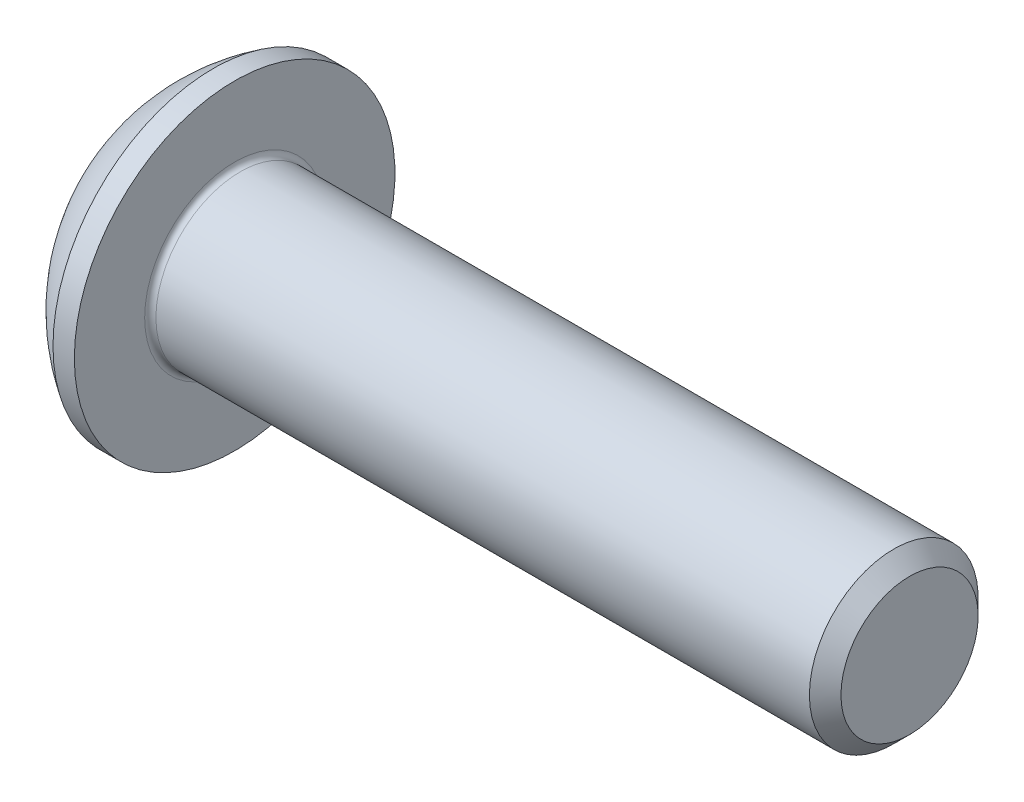
SolidWorks part; units mm, degrees
ref_plane "Plane1" through (0, 0, 0) normal (0, 0, 1) x (1, 0, 0)
ref_plane "Plane2" through (0, 0, 0) normal (0, 1, 0) x (1, 0, 0)
ref_plane "Plane3" through (0, 0, 0) normal (1, 0, 0) x (0, 0, -1)
sketch "BodySke" plane through (0, 0, 0) normal (0, 0, 1) x (1, 0, 0)
  line L0 (13.65, 0) -> (13.65, 1.2195)
  line L1 (13.3695, 1.5) -> (1.65, 1.5)
  line L2 (1.65, 1.5) -> (1.65, 2.85)
  line L3 (1.65, 2.85) -> (1.27, 2.85)
  line L4 (0, 0) -> (101.6, 0) construction
  line L5 (1.65, -2.85) -> (1.27, -2.85) construction
  line L6 (55.6768, -1.5) -> (1.65, -1.5) construction
  line L7 (13.65, 0) -> (0, 0)
  line L8 (0, 1.425) -> (0, -1.425) construction
  line L9 (0, 0) -> (0, 1.425)
  line L10 (13.65, 1.2195) -> (13.3695, 1.5)
  line L11 (13.65, -1.2195) -> (13.3695, -1.5) construction
  line L12 (2.15, 9.525) -> (2.15, -1.5) construction
  line L13 (1.65, 9.525) -> (1.65, -1.5) construction
  arc A1 (0, 1.425) -> (1.27, 2.85) centre (3.0334, 0) cw
  dimension "Diameter" = 3
  dimension "Length" = 12
  dimension "Head_dia" = 5.7
  dimension "D1" = 2.85
  dimension "Head_ht" = 1.65
  dimension "Head_side_ht" = 0.38
  dimension "Minor_dia" = 2.439
  dimension "Body_ch_ang" = 45
  dimension "Advance" = 0.5
  dimension "Thread_nom" = 12
revolve "BaseBody" add sketch "BodySke" angle 360 about L4
cosmetic thread "ThreadCosmetic" parameters "Thread_length"=11, "Thread_minor"=2.439
fillet "Fillet1" radius 0.1 1 edges at (1.65, 0, 1.5)
sketch "Sketch2" plane through (0, 0, 0) normal (0, 0, 1) x (1, 0, 0)
  line L0 (0, 1) -> (1.04, 1)
  line L1 (1.04, 1) -> (1.6174, 0)
  line L3 (1.6174, 0) -> (0, 0)
  line L4 (0, 0) -> (0, 1)
  line L5 (0, -1) -> (1.04, -1) construction
  line L6 (0, 0) -> (47.625, 0) construction
  dimension "D2" = 60
  dimension "PreBroach_depth" = 1.04
  dimension "PreBroach_dia" = 2
revolve "PreBroach" cut sketch "Sketch2" angle 360 about L6
sketch "Sketch3" plane through (0, 0, 0) normal (1, 0, 0) x (0, 0, -1)
  line L0 (-1, -0.5774) -> (-1, 0.5774)
  line L1 (-1, 0.5774) -> (0, 1.1547)
  line L2 (0, 1.1547) -> (1, 0.5774)
  line L3 (1, 0.5774) -> (1, -0.5774)
  line L4 (1, -0.5774) -> (0, -1.1547)
  line L5 (0, -1.1547) -> (-1, -0.5774)
  dimension "Hex_size" = 2
  dimension "D3" = 2
  dimension "D1" = 1
  dimension "D2" = 1
extrude "Hex" cut sketch "Sketch3" along normal blind 1.04
sketch "ThdSchSke" plane through (0, 0, 0) normal (0, 0, 1) x (1, 0, 0)
  line L0 (2.65, -1.2195) -> (2.4536, -1.5)
  line L1 (2.65, -1.2195) -> (2.8464, -1.5)
  line L2 (2.8464, -1.5) -> (2.8464, -1.875)
  line L3 (-3.175, 0) -> (5.1513, 0) construction
  line L5 (2.8464, -1.875) -> (2.4536, -1.875)
  line L6 (2.4536, -1.875) -> (2.4536, -1.5)
  dimension "Diameter" = 3
  dimension "Thread_minor" = 2.439
  dimension "SideAngle" = 55
  dimension "VeeAngle" = 70
  dimension "Overcut" = 3.75
  dimension "Start" = 2.65
revolve "ThreadSchematic" [suppressed] cut sketch "ThdSchSke" angle 360 about L3
pattern_linear "ThdSchPat" [suppressed]
equation "\"D1@BodySke\" = \"Head_dia@BodySke\" * .5"
equation "\"Thread_minor@ThreadCosmetic\" = \"Minor_dia@BodySke\""
equation "\"D1@Sketch3\" = \"Hex_size@Sketch3\" / 2"
equation "\"D2@Sketch3\" = \"D1@Sketch3\""
equation "\"D3@Sketch3\" = \"Hex_size@Sketch3\""
equation "\"Thread_length@ThreadCosmetic\" = ((sgn( (\"Length@BodySke\" - \"Advance@BodySke\" * 2.0) - \"Thread_nom@BodySke\" )-1)*( (\"Length@BodySke\" - \"Advance@BodySke\" * 2.0) - \"Thread_nom@BodySke\" ))/-2+ \"Thread_nom@BodySke\""
equation "\"Thread_minor@ThdSchSke\" = \"Minor_dia@BodySke\""
equation "\"Diameter@ThdSchSke\" = \"Diameter@BodySke\""
equation "\"Overcut@ThdSchSke\" = \"Diameter@BodySke\" * 1.25"
equation "\"Start@ThdSchSke\" = \"Head_ht@BodySke\" + \"Length@BodySke\" - \"Thread_length@ThreadCosmetic\"  '---Non-countersunk---"
equation "\"Num_threads@ThdSchPat\" = int( \"Thread_length@ThreadCosmetic\" / \"Advance@BodySke\" + 0.999 )  + 1"
equation "\"Advance@ThdSchPat\" = \"Thread_length@ThreadCosmetic\" /  (\"Num_threads@ThdSchPat\" - 1) 'relax it"
equation "\"Num_threads@ThdSchPat\" = \"Num_threads@ThdSchPat\" - sgn( \"Num_threads@ThdSchPat\" - 1) '---chamfered tips only---"
